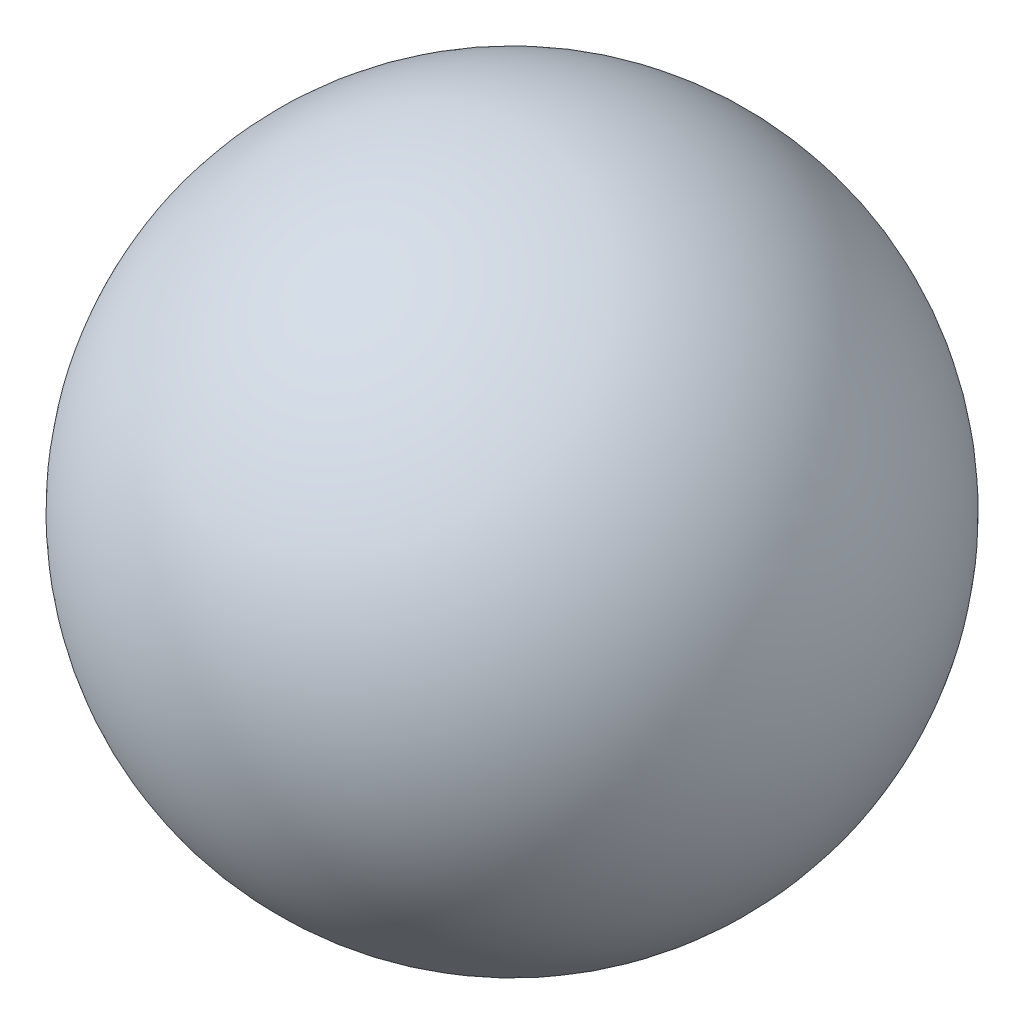
SolidWorks part; units mm, degrees
ref_plane "Front Plane" through (0, 0, 0) normal (0, 0, 1) x (1, 0, 0)
ref_plane "Top Plane" through (0, 0, 0) normal (0, 1, 0) x (1, 0, 0)
ref_plane "Right Plane" through (0, 0, 0) normal (1, 0, 0) x (0, 0, -1)
ref_plane "Plane1" through (0, 0, 1.6223) normal (0, 0, 1) x (1, 0, 0)
sketch "Sketch1" plane through (0, 0, 1.6223) normal (0, 0, 1) x (1, 0, 0)
  line L0 (3.643, -2.5) -> (6.343, -2.5)
  line L1 (3.643, -2.5) -> (6.343, -2.5) construction
  arc A0 (6.343, -2.5) -> (3.643, -2.5) centre (4.993, -2.5) ccw
revolve "Revolve1" add sketch "Sketch1" angle 360 about L1
